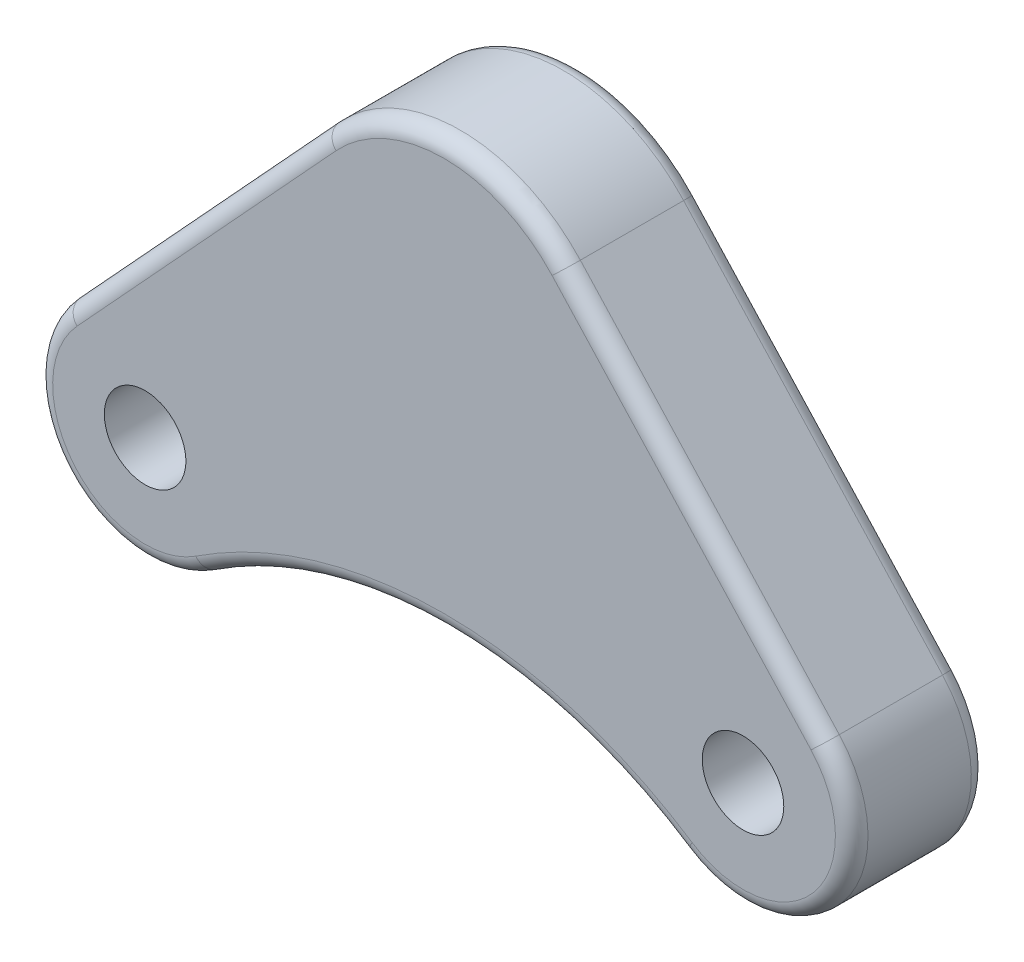
SolidWorks part; units mm, degrees
material "Cedar"
ref_plane "Front Plane" through (0, 0, 0) normal (0, 0, 1) x (1, 0, 0)
ref_plane "Top Plane" through (0, 0, 0) normal (0, 1, 0) x (1, 0, 0)
ref_plane "Right Plane" through (0, 0, 0) normal (1, 0, 0) x (0, 0, -1)
sketch "Sketch1" plane through (0, 0, 0) normal (0, 0, 1) x (1, 0, 0)
  line L0 (0, -63.4217) -> (0, 47.8045) construction
  line L1 (22.0754, 20.3144) -> (69.717, -31.4571)
  line L2 (-22.0754, 20.3144) -> (-69.717, -31.4571)
  arc A0 (-22.0754, 20.3144) -> (22.0754, 20.3144) centre (0, 0) cw
  arc A1 (69.717, -31.4571) -> (44, -61.7033) centre (55, -45) cw
  arc A2 (44, -61.7033) -> (-44, -61.7033) centre (0, -128.5165) ccw
  circle A3 centre (55, -45) radius 7.5
  circle A4 centre (-55, -45) radius 7.5
  arc A5 (-69.717, -31.4571) -> (-44, -61.7033) centre (-55, -45) ccw
  dimension "D1" = 30
  dimension "D2" = 20
  dimension "D3" = 15
  dimension "D6" = 80
  dimension "D4" = 55
  dimension "D5" = 45
extrude "Boss-Extrude2" add sketch "Sketch1" along normal blind 25
fillet "Fillet2" radius 3 12 edges at (0, 30, 25) (45.8962, -5.5713, 25) (70.2369, -57.9552, 25) (0, -48.5165, 25) (-70.2369, -57.9552, 25) (-45.8962, -5.5713, 25) (70.2369, -57.9552, 0) (0, -48.5165, 0) (-70.2369, -57.9552, 0) (-45.8962, -5.5713, 0) (0, 30, 0) (45.8962, -5.5713, 0)
